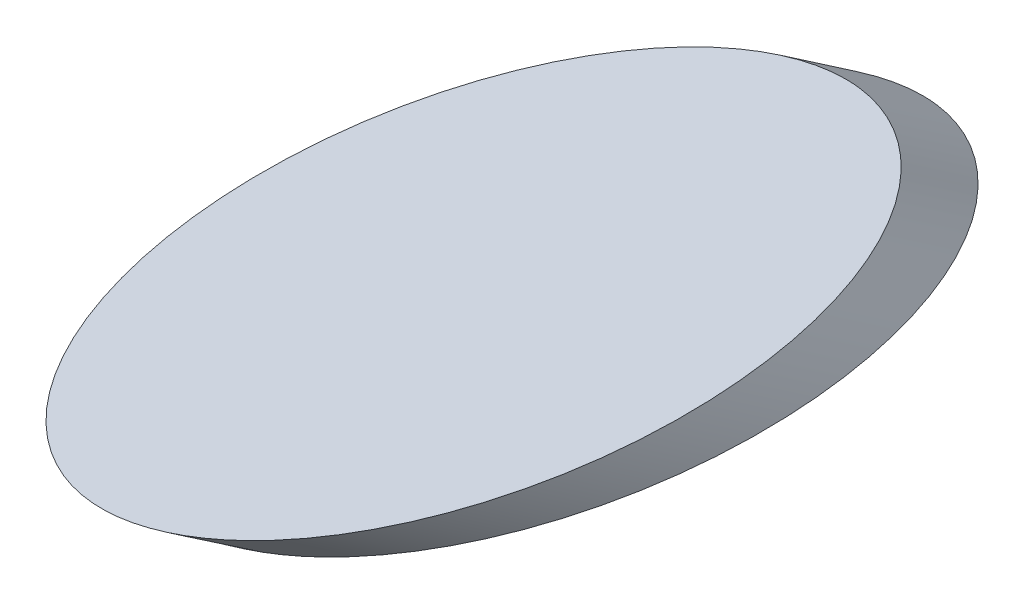
SolidWorks part; units mm, degrees
ref_plane "前视基准面" through (0, 0, 0) normal (0, 0, 1) x (1, 0, 0)
ref_plane "上视基准面" through (0, 0, 0) normal (0, 1, 0) x (1, 0, 0)
ref_plane "右视基准面" through (0, 0, 0) normal (1, 0, 0) x (0, 0, -1)
sketch "草图1" plane through (0, 0, 0) normal (0, 1, 0) x (1, 0, 0)
  ellipse E0 centre (0, 0) end of major axis (0, 14.115) minor radius 8
sketch "草图2" plane through (0, 0, 0) normal (1, 0, 0) x (0, 0, -1)
  line L0 (-14.115, 0) -> (-11.1977, -2)
  line L1 (14.115, 0) -> (-14.115, 0) construction
  line L2 (-16.0371, -2) -> (12.8274, -2) construction
  line L3 (14.115, 0) -> (-14.115, 0) construction
  point P1 (-12.8756, -2)
  point P7 (0, 0)
  point P8 (0, 0)
  dimension "D1" = 34.433
  dimension "D2" = 2
sweep "扫描1" add profiles "草图1" path "草图2"
